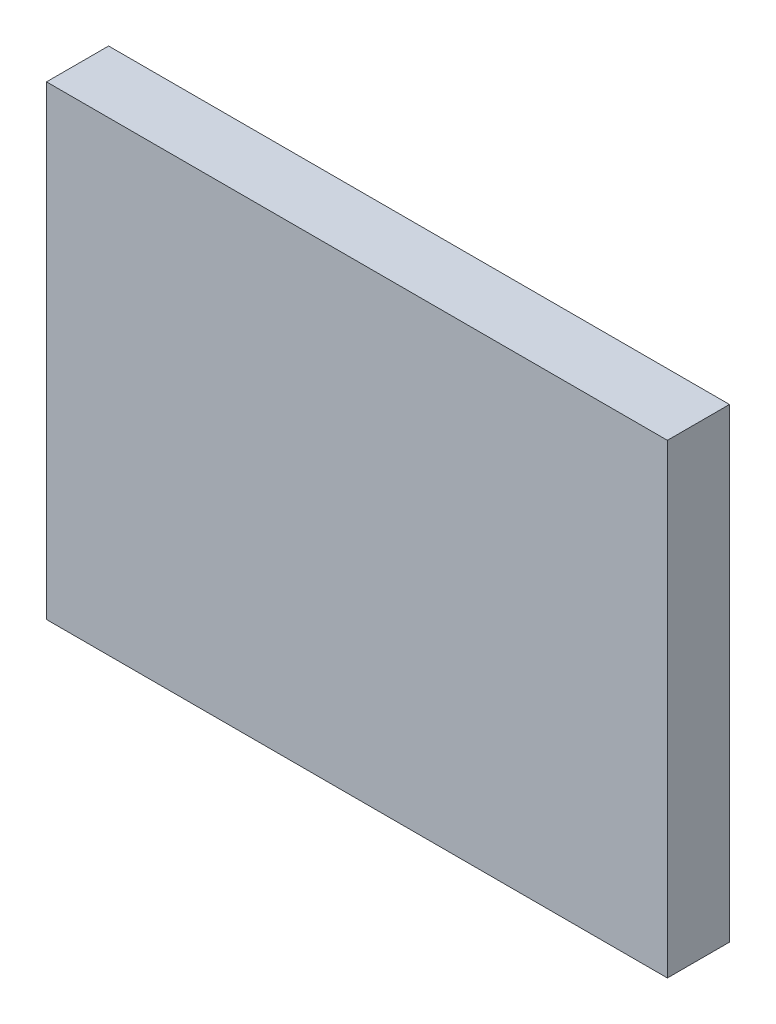
SolidWorks part; units mm, degrees
ref_plane "Front Plane" through (0, 0, 0) normal (0, 0, 1) x (1, 0, 0)
ref_plane "Top Plane" through (0, 0, 0) normal (0, 1, 0) x (1, 0, 0)
ref_plane "Right Plane" through (0, 0, 0) normal (1, 0, 0) x (0, 0, -1)
sketch "Sketch1" plane through (0, 0, 0) normal (0, 0, 1) x (1, 0, 0)
  line L1 (0, 0) -> (25.4, 0)
  line L2 (0, 0) -> (0, 19.05)
  line L3 (0, 19.05) -> (25.4, 19.05)
  line L4 (25.4, 0) -> (25.4, 19.05)
  dimension "D1" = 19.05
  dimension "D2" = 25.4
extrude "Boss-Extrude1" add sketch "Sketch1" along normal blind 2.54
